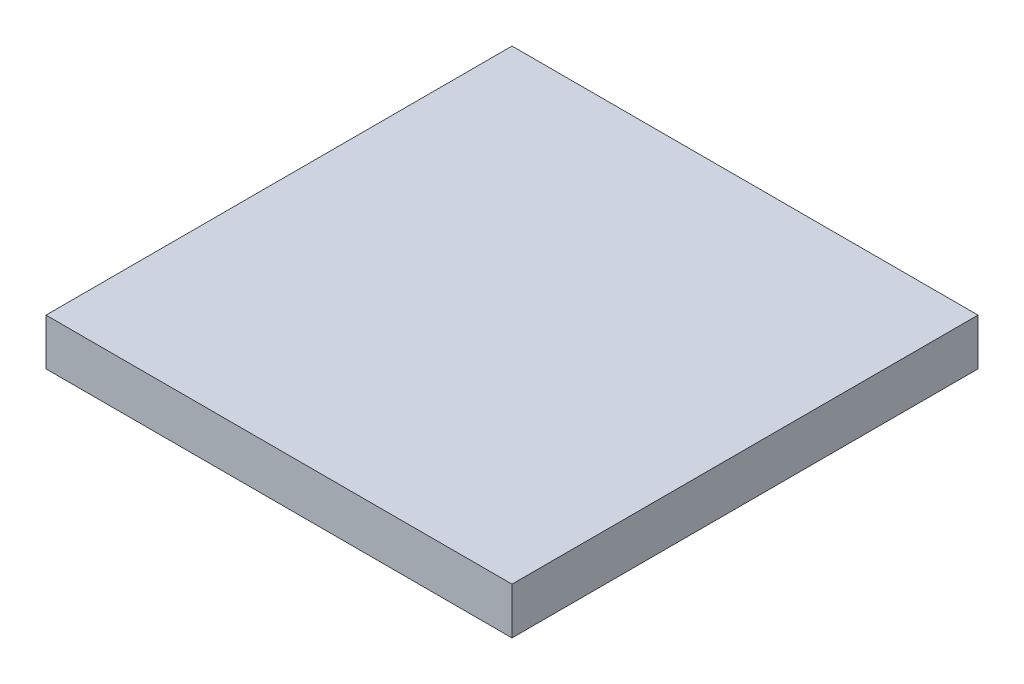
SolidWorks part; units mm, degrees
ref_plane "Front Plane" through (0, 0, 0) normal (0, 0, 1) x (1, 0, 0)
ref_plane "Top Plane" through (0, 0, 0) normal (0, 1, 0) x (1, 0, 0)
ref_plane "Right Plane" through (0, 0, 0) normal (1, 0, 0) x (0, 0, -1)
sketch "Sketch1" plane through (0, 0, 0) normal (0, 1, 0) x (1, 0, 0)
  line L0 (-50, 0) -> (-50, 35)
  line L1 (-50, 35) -> (50, 35)
  line L3 (-50, -65) -> (50, -65)
  line L5 (50, 35) -> (50, 0)
  line L6 (50, 0) -> (50, -65)
  line L7 (-50, -65) -> (-50, 0)
  point P0 (0, 0)
  dimension "D1" = 100
  dimension "D2" = 35
  dimension "D3" = 65
  dimension "D4" = 0
  dimension "D5" = 50
extrude "Boss-Extrude1" add sketch "Sketch1" along normal blind 10
sketch "Sketch2" plane through (0, 0, 0) normal (0, 1, 0) x (1, 0, 0)
  circle A0 centre (0, 0) radius 1
  dimension "D1" = 2
extrude "Cut-Extrude1" cut sketch "Sketch2" along normal blind 0.0001
